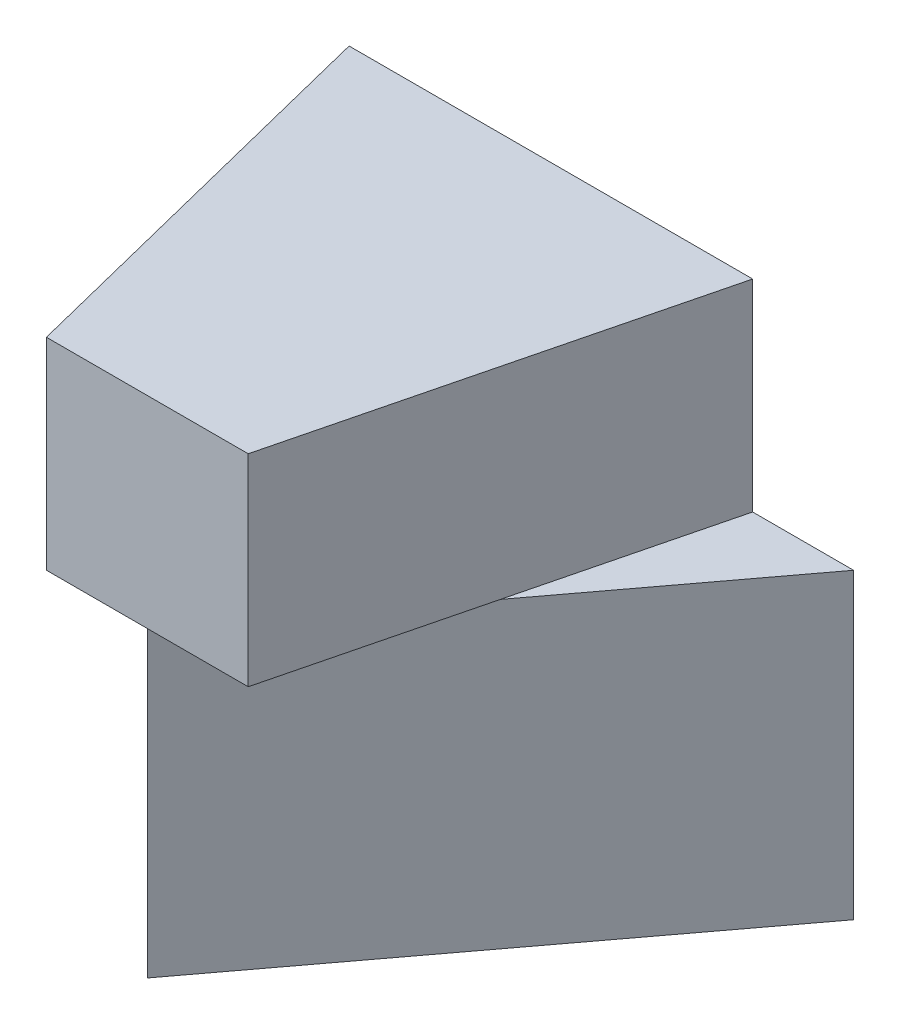
SolidWorks part; units mm, degrees
ref_plane "Front Plane" through (0, 0, 0) normal (0, 0, 1) x (1, 0, 0)
ref_plane "Top Plane" through (0, 0, 0) normal (0, 1, 0) x (1, 0, 0)
ref_plane "Right Plane" through (0, 0, 0) normal (1, 0, 0) x (0, 0, -1)
sketch "Sketch1" plane through (0, 0, 0) normal (0, 1, 0) x (1, 0, 0)
  line L0 (0, 0) -> (-3, 4)
  line L1 (-3, 4) -> (3, 4)
  line L2 (3, 4) -> (0, 0)
  dimension "D1" = 6
  dimension "D2" = 3
  dimension "D3" = 4
extrude "Boss-Extrude1" add sketch "Sketch1" along normal blind 3
sketch "Sketch2" plane through (0, 3, 0) normal (0, 1, 0) x (1, 0, 0)
  line L0 (2, 4) -> (1, 0)
  line L1 (3, 4) -> (-3, 4) construction
  line L2 (-2, 4) -> (2, 4)
  line L3 (1, 0) -> (-1, 0)
  line L4 (-1, 0) -> (-2, 4)
  dimension "D1" = 4
  dimension "D2" = 2
  dimension "D3" = 1
  dimension "D4" = 1
extrude "Boss-Extrude2" add sketch "Sketch2" along normal blind 2
